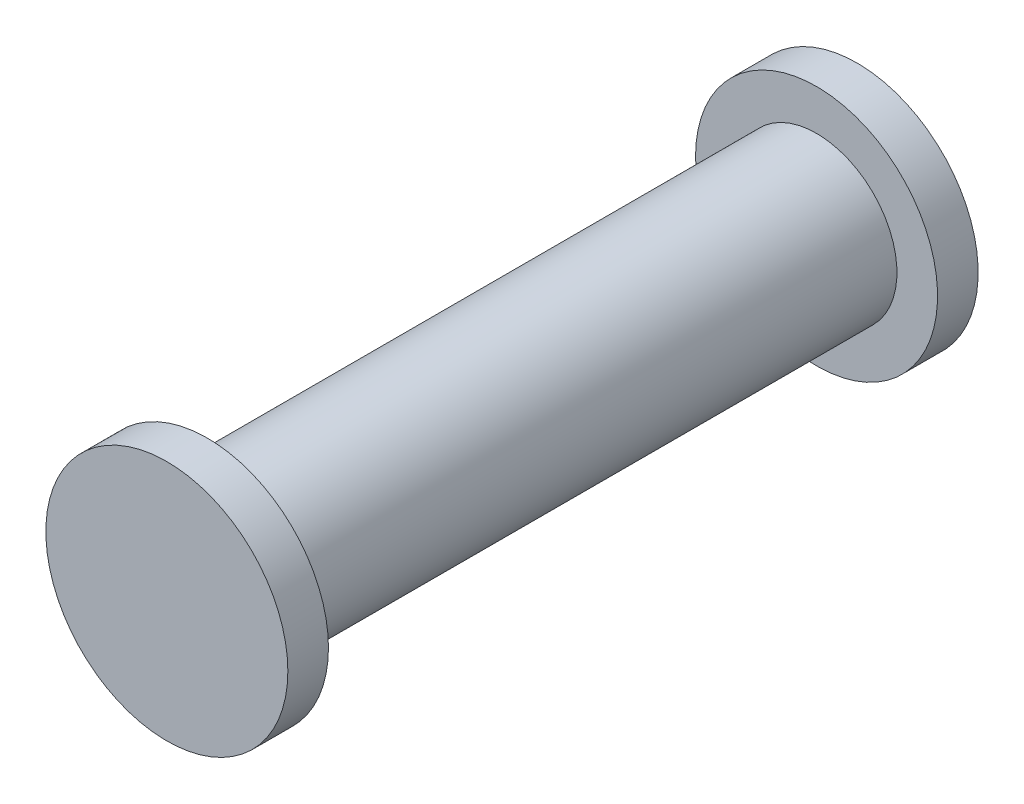
SolidWorks part; units mm, degrees
ref_plane "Front Plane" through (0, 0, 0) normal (0, 0, 1) x (1, 0, 0)
ref_plane "Top Plane" through (0, 0, 0) normal (0, 1, 0) x (1, 0, 0)
ref_plane "Right Plane" through (0, 0, 0) normal (1, 0, 0) x (0, 0, -1)
sketch "Sketch1" plane through (0, 0, 0) normal (0, 0, 1) x (1, 0, 0)
  circle A0 centre (0, 0) radius 4.95
  dimension "D1" = 9.9
extrude "Boss-Extrude1" add sketch "Sketch1" along normal blind 37.5
sketch "Sketch2" plane through (0, 0, 0) normal (0, 0, -1) x (-1, 0, 0)
  circle A2 centre (0, 0) radius 7.45
  circle A3 centre (0, 0) radius 7.45
  dimension "D1" = 2.5
extrude "Boss-Extrude2" add sketch "Sketch2" along normal blind 2.5
sketch "Sketch3" plane through (0, 0, 37.5) normal (0, 0, 1) x (1, 0, 0)
  circle A2 centre (0, 0) radius 7.45
  circle A3 centre (0, 0) radius 7.45
  dimension "D1" = 2.5
extrude "Boss-Extrude3" add sketch "Sketch3" along normal blind 2.5
